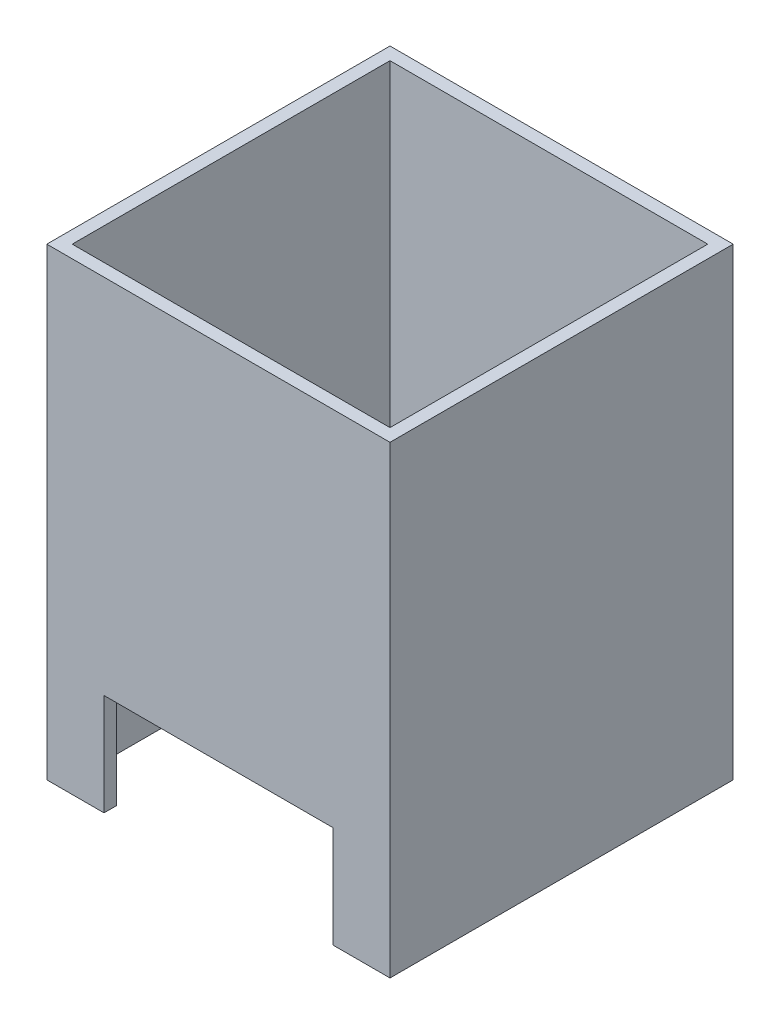
SolidWorks part; units mm, degrees
ref_plane "Front Plane" through (0, 0, 0) normal (0, 0, 1) x (1, 0, 0)
ref_plane "Top Plane" through (0, 0, 0) normal (0, 1, 0) x (1, 0, 0)
ref_plane "Right Plane" through (0, 0, 0) normal (1, 0, 0) x (0, 0, -1)
sketch "Sketch1" plane through (0, 0, 0) normal (0, 1, 0) x (1, 0, 0)
  line L1 (-25, -25) -> (25, -25)
  line L2 (-25, -25) -> (-25, 25)
  line L3 (-25, 25) -> (25, 25)
  line L4 (25, -25) -> (25, 25)
  line L5 (-25, -25) -> (25, 25) construction
  line L6 (-25, 25) -> (25, -25) construction
  line L7 (-27, -27) -> (27, -27)
  line L8 (-27, -27) -> (-27, 27)
  line L9 (-27, 27) -> (27, 27)
  line L10 (27, -27) -> (27, 27)
  line L11 (-27, -27) -> (27, 27) construction
  line L12 (-27, 27) -> (27, -27) construction
  point P0 (0, 0)
  point P6 (0, 0)
  dimension "D1" = 50
  dimension "D2" = 50
  dimension "D3" = 2
  dimension "D4" = 2
extrude "Boss-Extrude1" add sketch "Sketch1" along normal blind 22
sketch "Sketch2" plane through (0, 22, 0) normal (0, 1, 0) x (1, 0, 0)
  line L1 (-27, -27) -> (27, -27)
  line L2 (-27, -27) -> (-27, 27)
  line L3 (-27, 27) -> (27, 27)
  line L4 (27, -27) -> (27, 27)
  line L5 (-27, -27) -> (27, 27) construction
  line L6 (-27, 27) -> (27, -27) construction
  point P0 (0, 0)
extrude "Boss-Extrude2" add sketch "Sketch2" along normal blind 1
sketch "Sketch3" plane through (0, 23, 0) normal (0, 1, 0) x (1, 0, 0)
  circle A0 centre (0, 0) radius 6
  dimension "D1" = 12
extrude "Cut-Extrude1" cut sketch "Sketch3" against normal through all
sketch "Sketch4" plane through (0, 23, 0) normal (0, 1, 0) x (1, 0, 0)
  line L0 (27, -27) -> (27, 27) construction
  line L1 (-27, 27) -> (27, 27)
  line L2 (-27, 27) -> (-27, 25)
  line L3 (-27, 25) -> (27, 25)
  line L4 (27, 27) -> (27, 25)
  line L5 (-27, -27) -> (27, -27) construction
  line L6 (27, 27) -> (25, 27)
  line L7 (27, 27) -> (27, -27)
  line L8 (27, -27) -> (25, -27)
  line L9 (25, 27) -> (25, -27)
  line L11 (-27, -27) -> (27, -27)
  line L12 (-27, -27) -> (-27, -25)
  line L13 (-27, -25) -> (27, -25)
  line L14 (27, -27) -> (27, -25)
  line L15 (-27, 27) -> (-25, 27)
  line L16 (-27, 27) -> (-27, -27)
  line L17 (-27, -27) -> (-25, -27)
  line L18 (-25, 27) -> (-25, -27)
  line M10 (27, -27) -> (27, 27)
  line M11 (27, 27) -> (-27, 27)
  line M12 (-27, 27) -> (-27, -27)
  line M13 (-27, -27) -> (27, -27)
  dimension "D1" = 2
  dimension "D2" = 2
  dimension "D3" = 2
  dimension "D4" = 2
extrude "Boss-Extrude3" add sketch "Sketch4" along normal blind 50 contours L18 L3 L13 M12 | L18 L13 M12 M13 | L13 L18 L11 L9 | L13 L9 M13 M10 | L9 L13 L7 L3 | L9 L3 M11 M10 | L1 L18 L3 L9 | L18 L3 M11 M12
sketch "Sketch5" plane through (0, 22, 0) normal (0, -1, 0) x (1, 0, 0)
  line L1 (-16.5, -16.5) -> (16.5, -16.5)
  line L2 (-16.5, -16.5) -> (-16.5, 16.5)
  line L3 (-16.5, 16.5) -> (16.5, 16.5)
  line L4 (16.5, -16.5) -> (16.5, 16.5)
  line L5 (-16.5, -16.5) -> (16.5, 16.5) construction
  line L6 (-16.5, 16.5) -> (16.5, -16.5) construction
  point P0 (0, 0)
  dimension "D1" = 33
  dimension "D2" = 33
extrude "Cut-Extrude2" cut sketch "Sketch5" against normal through all
sketch "Sketch6" plane through (0, 0, 27) normal (0, 0, 1) x (1, 0, 0)
  line L0 (27, 73) -> (27, 0) construction
  line L1 (-18, 0) -> (18, 0)
  line L2 (-18, 0) -> (-18, 16)
  line L3 (-18, 16) -> (18, 16)
  line L4 (18, 0) -> (18, 16)
  line L5 (-27, 73) -> (-27, 0) construction
  dimension "D1" = 16
  dimension "D2" = 9
  dimension "D3" = 9
extrude "Cut-Extrude3" cut sketch "Sketch6" against normal up to next
